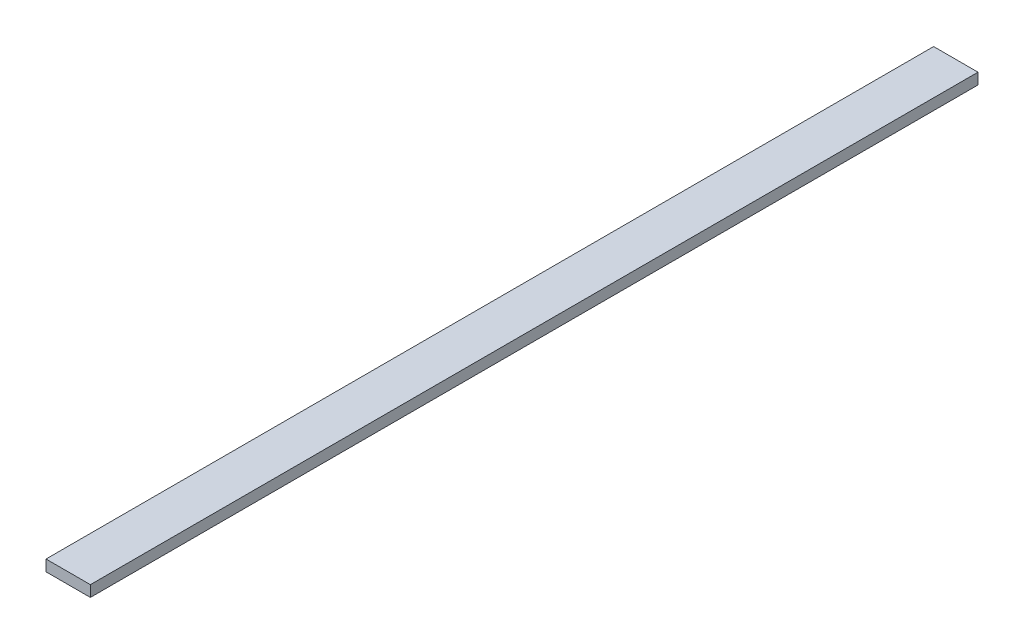
SolidWorks part; units mm, degrees
material "Gray Cast Iron"
ref_plane "Front Plane" through (0, 0, 0) normal (0, 0, 1) x (1, 0, 0)
ref_plane "Top Plane" through (0, 0, 0) normal (0, 1, 0) x (1, 0, 0)
ref_plane "Right Plane" through (0, 0, 0) normal (1, 0, 0) x (0, 0, -1)
sketch "Sketch1" plane through (0, 0, 0) normal (0, 1, 0) x (1, 0, 0)
  line L5 (-21.7938, 9954.8369) -> (478.2062, 9954.8369)
  line L6 (-21.7938, 9954.8369) -> (-21.7938, -45.1631)
  line L7 (-21.7938, -45.1631) -> (478.2062, -45.1631)
  line L8 (478.2062, 9954.8369) -> (478.2062, -45.1631)
  dimension "D1" = 10000
  dimension "D2" = 500
  dimension "D3" = 478.2062
  dimension "D4" = 9954.8369
extrude "Boss-Extrude1" add sketch "Sketch1" along normal blind 125
